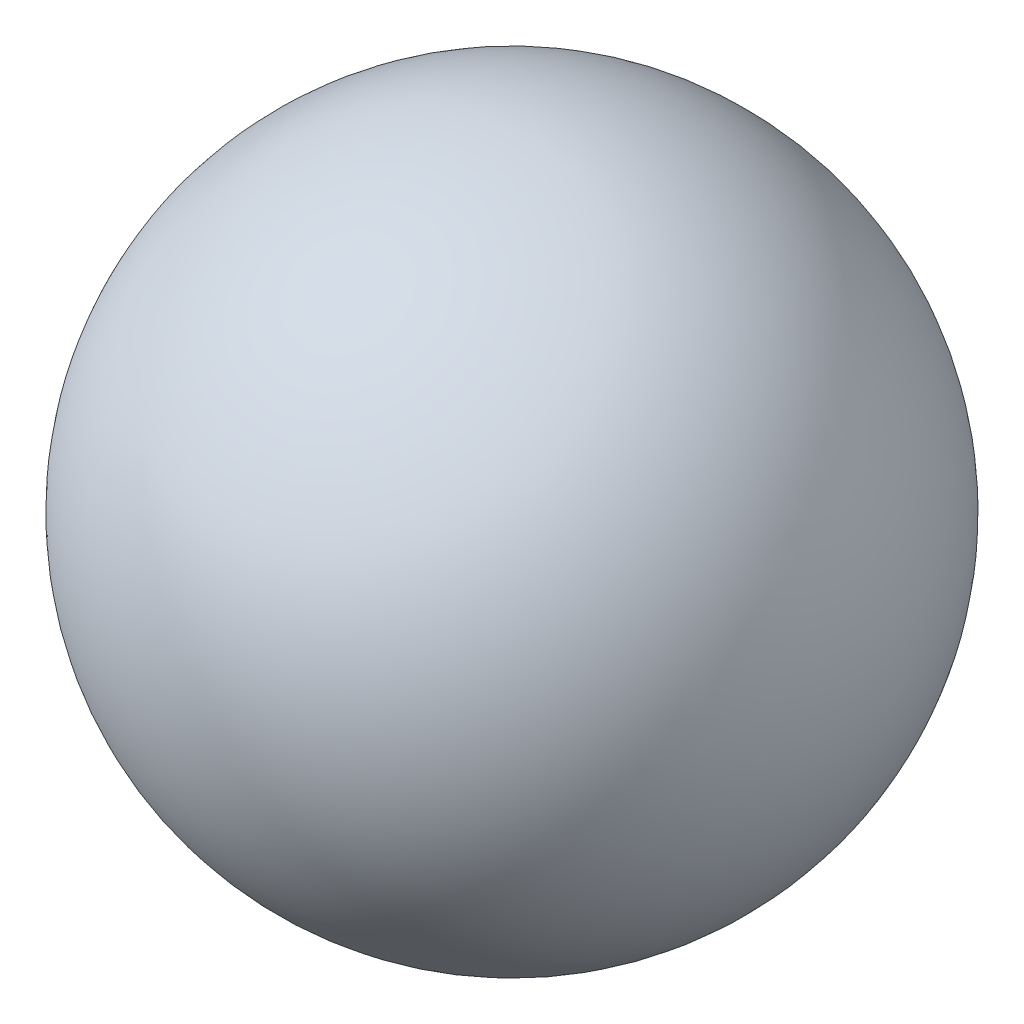
SolidWorks part; units mm, degrees
ref_plane "Front Plane" through (0, 0, 0) normal (0, 0, 1) x (1, 0, 0)
ref_plane "Top Plane" through (0, 0, 0) normal (0, 1, 0) x (1, 0, 0)
ref_plane "Right Plane" through (0, 0, 0) normal (1, 0, 0) x (0, 0, -1)
sketch "Sketch1" plane through (0, 0, 0) normal (0, 0, 1) x (1, 0, 0)
  line L0 (-6.275, 0) -> (6.275, 0)
  arc A0 (6.275, 0) -> (-6.275, 0) centre (0, 0) ccw
  dimension "D1" = 12.55
revolve "Revolve1" add sketch "Sketch1" angle 360 about L0
